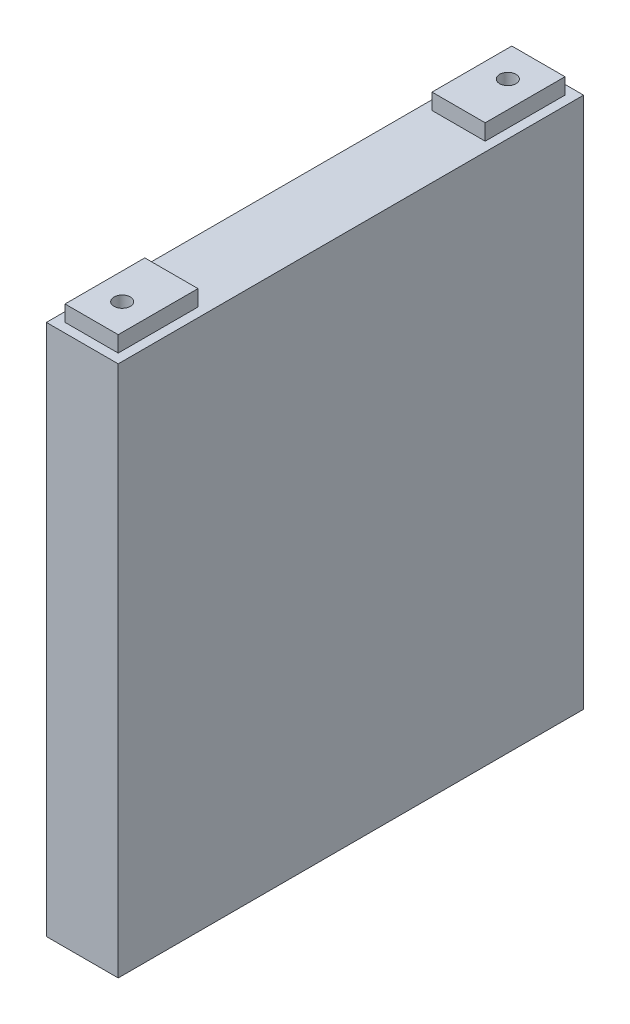
SolidWorks part; units mm, degrees
ref_plane "Front Plane" through (0, 0, 0) normal (0, 0, 1) x (1, 0, 0)
ref_plane "Top Plane" through (0, 0, 0) normal (0, 1, 0) x (1, 0, 0)
ref_plane "Right Plane" through (0, 0, 0) normal (1, 0, 0) x (0, 0, -1)
sketch "Sketch1" plane through (0, 0, 0) normal (0, 1, 0) x (1, 0, 0)
  line L1 (-13.5, -87.5) -> (13.5, -87.5)
  line L2 (-13.5, -87.5) -> (-13.5, 87.5)
  line L3 (-13.5, 87.5) -> (13.5, 87.5)
  line L4 (13.5, -87.5) -> (13.5, 87.5)
  line L5 (-13.5, -87.5) -> (13.5, 87.5) construction
  line L6 (-13.5, 87.5) -> (13.5, -87.5) construction
  point P0 (0, 0)
  dimension "D1" = 27
  dimension "D2" = 175
extrude "Boss-Extrude1" add sketch "Sketch1" along normal blind 200
sketch "Sketch2" plane through (0, 200, 0) normal (0, 1, 0) x (1, 0, 0)
  line L0 (0, 0) -> (0, 69) construction
  line L1 (0, 0) -> (0, -69) construction
  line L2 (13.5, 87.5) -> (-13.5, 87.5) construction
  line L3 (-10, -84) -> (10, -84)
  line L4 (-10, -84) -> (-10, -54)
  line L5 (-10, -54) -> (10, -54)
  line L6 (10, -84) -> (10, -54)
  line L7 (-10, -84) -> (10, -54) construction
  line L8 (-10, -54) -> (10, -84) construction
  line L9 (-10, 54) -> (10, 54)
  line L10 (-10, 54) -> (-10, 84)
  line L11 (-10, 84) -> (10, 84)
  line L12 (10, 54) -> (10, 84)
  line L13 (-10, 54) -> (10, 84) construction
  line L14 (-10, 84) -> (10, 54) construction
  line L15 (0, 69) -> (0, 72.5) construction
  line L16 (0, -69) -> (0, -72.5) construction
  circle A0 centre (0, -72.5) radius 3.0719
  circle A1 centre (0, 72.5) radius 3.0719
  dimension "D4" = 6.1438
  dimension "D1" = 30
  dimension "D2" = 20
  dimension "D3" = 3.5
  dimension "D5" = 145
extrude "Boss-Extrude2" add sketch "Sketch2" along normal blind 6
